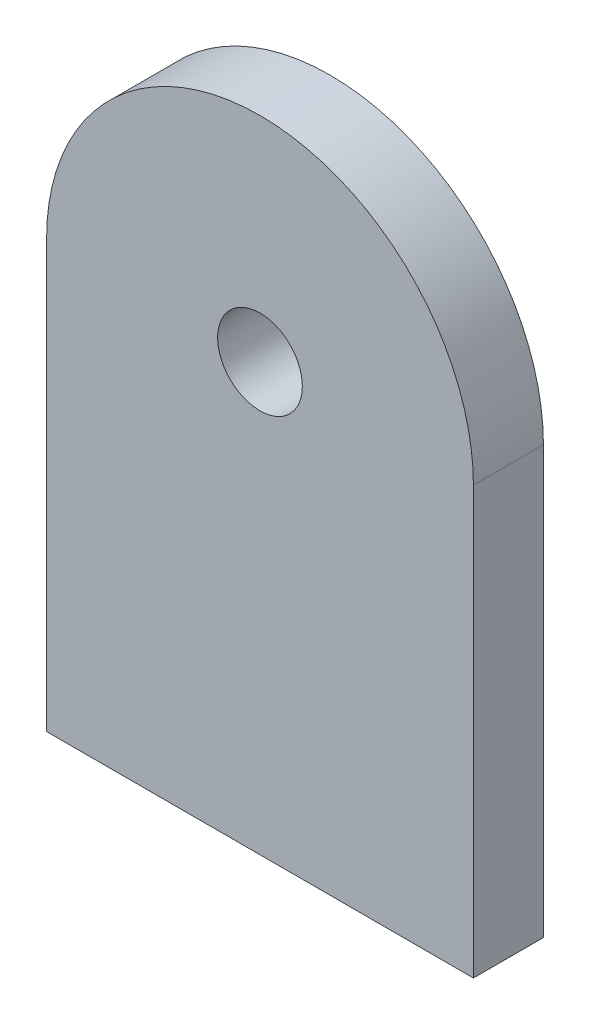
SolidWorks part; units mm, degrees
ref_plane "Front Plane" through (0, 0, 0) normal (0, 0, 1) x (1, 0, 0)
ref_plane "Top Plane" through (0, 0, 0) normal (0, 1, 0) x (1, 0, 0)
ref_plane "Right Plane" through (0, 0, 0) normal (1, 0, 0) x (0, 0, -1)
sketch "Sketch1" plane through (0, 0, 0) normal (0, 0, 1) x (1, 0, 0)
  line L0 (0, 0) -> (0, -30.48) construction
  line L1 (-15.24, -30.48) -> (15.24, -30.48)
  line L2 (15.24, -30.48) -> (15.24, 0)
  line L3 (-15.24, -30.48) -> (-15.24, 0)
  arc A0 (15.24, 0) -> (-15.24, 0) centre (0, 0) ccw
  circle A1 centre (0, 0) radius 3.025
  point P8 (0, -30.48)
  dimension "D1" = 6.05
  dimension "D2" = 30.48
  dimension "D3" = 30.48
extrude "Boss-Extrude1" add sketch "Sketch1" along normal mid plane 5
